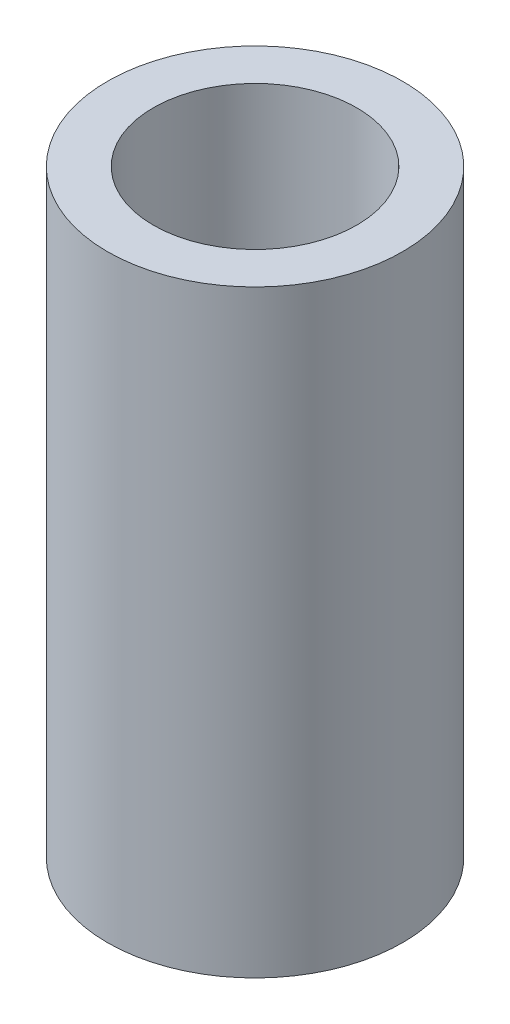
SolidWorks part; units mm, degrees
ref_plane "Front Plane" through (0, 0, 0) normal (0, 0, 1) x (1, 0, 0)
ref_plane "Top Plane" through (0, 0, 0) normal (0, 1, 0) x (1, 0, 0)
ref_plane "Right Plane" through (0, 0, 0) normal (1, 0, 0) x (0, 0, -1)
sketch "Sketch1" plane through (0, 0, 0) normal (0, 1, 0) x (1, 0, 0)
  circle A0 centre (0, 0) radius 7.4
  dimension "D1" = 14.8
extrude "Boss-Extrude1" add sketch "Sketch1" along normal blind 30
hole_wizard "M12x1.75 Tapped Hole1" positions "Sketch2" profile "Sketch3" tap size "M12x1.75" standard "ANSI Metric" end condition through all
sketch "Sketch2" plane through (0, 30, 0) normal (0, 1, 0) x (1, 0, 0)
  point P0 (0, 0)
sketch "Sketch3" plane through (0, 30, 0) normal (1, 0, 0) x (0, 0, 1)
  line L0 (0, 0) -> (0, 30)
  line L1 (0, 30) -> (5.1, 30)
  line L2 (5.1, 30) -> (5.1, 0)
  line L5 (5.1, 0) -> (0, 0)
  line L11 (0, -6.35) -> (0, 107.95) construction
  dimension "Thru Tap Drill Dia." = 10.2
  dimension "Thru Tap Drill Depth" = 30
cosmetic thread "Hole Thread1"
